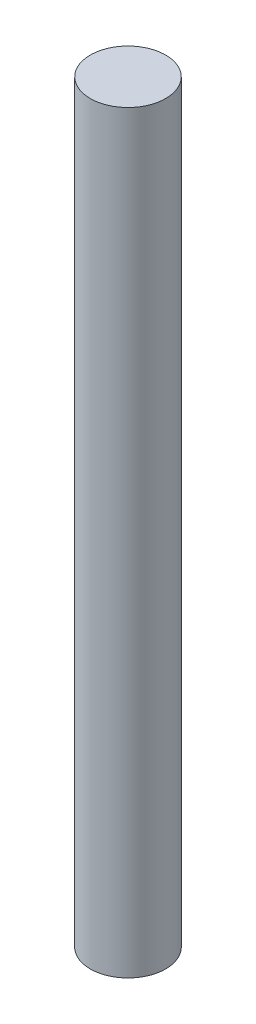
SolidWorks part; units mm, degrees
ref_plane "Front Plane" through (0, 0, 0) normal (0, 0, 1) x (1, 0, 0)
ref_plane "Top Plane" through (0, 0, 0) normal (0, 1, 0) x (1, 0, 0)
ref_plane "Right Plane" through (0, 0, 0) normal (1, 0, 0) x (0, 0, -1)
sketch "Sketch1" plane through (0, 0, 0) normal (0, 1, 0) x (1, 0, 0)
  circle A0 centre (0, 0) radius 30
  dimension "D1" = 60
extrude "Boss-Extrude1" add sketch "Sketch1" along normal blind 600
